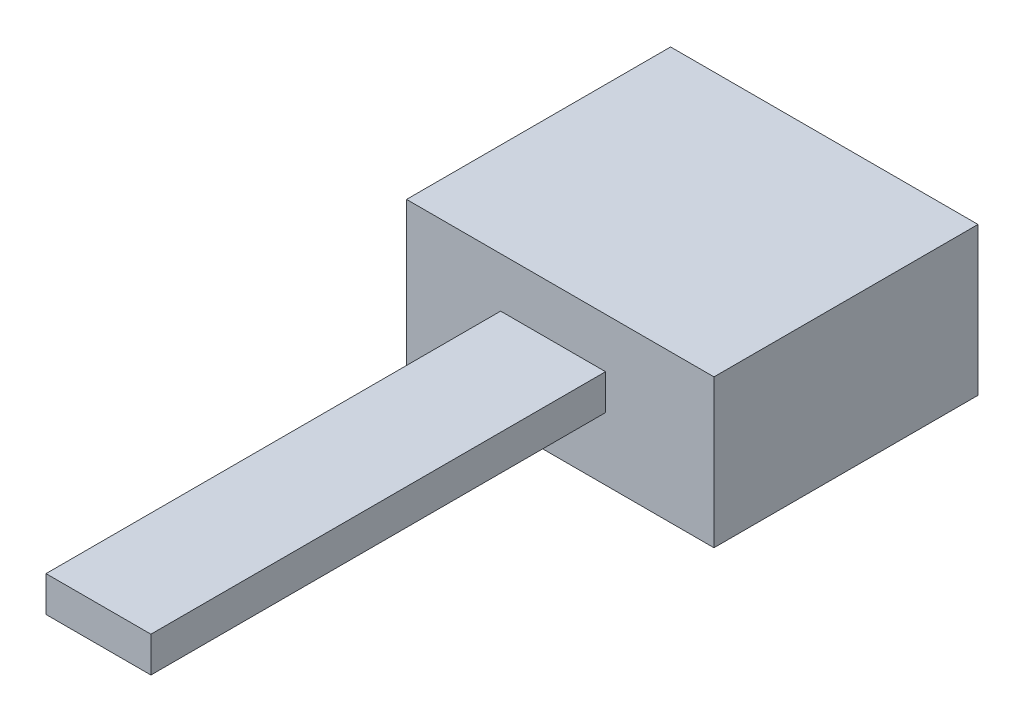
SolidWorks part; units mm, degrees
ref_plane "Front Plane" through (0, 0, 0) normal (0, 0, 1) x (1, 0, 0)
ref_plane "Top Plane" through (0, 0, 0) normal (0, 1, 0) x (1, 0, 0)
ref_plane "Right Plane" through (0, 0, 0) normal (1, 0, 0) x (0, 0, -1)
sketch "Sketch1" plane through (0, 0, 0) normal (0, 1, 0) x (1, 0, 0)
  line L1 (0, 0) -> (44.6532, 0)
  line L2 (0, 0) -> (0, 38.354)
  line L3 (0, 38.354) -> (44.6532, 38.354)
  line L4 (44.6532, 0) -> (44.6532, 38.354)
  dimension "D1" = 44.6532
  dimension "D2" = 38.354
extrude "Boss-Extrude1" add sketch "Sketch1" along normal blind 21.5
sketch "Sketch2" plane through (0, 0, 0) normal (0, 0, 1) x (1, 0, 0)
  line L1 (13.6673, 14.2781) -> (28.9073, 14.2781)
  line L2 (13.6673, 14.2781) -> (13.6673, 9.1361)
  line L3 (13.6673, 9.1361) -> (28.9073, 9.1361)
  line L4 (28.9073, 14.2781) -> (28.9073, 9.1361)
  dimension "D1" = 15.24
extrude "Boss-Extrude2" add sketch "Sketch2" along normal blind 66.04
